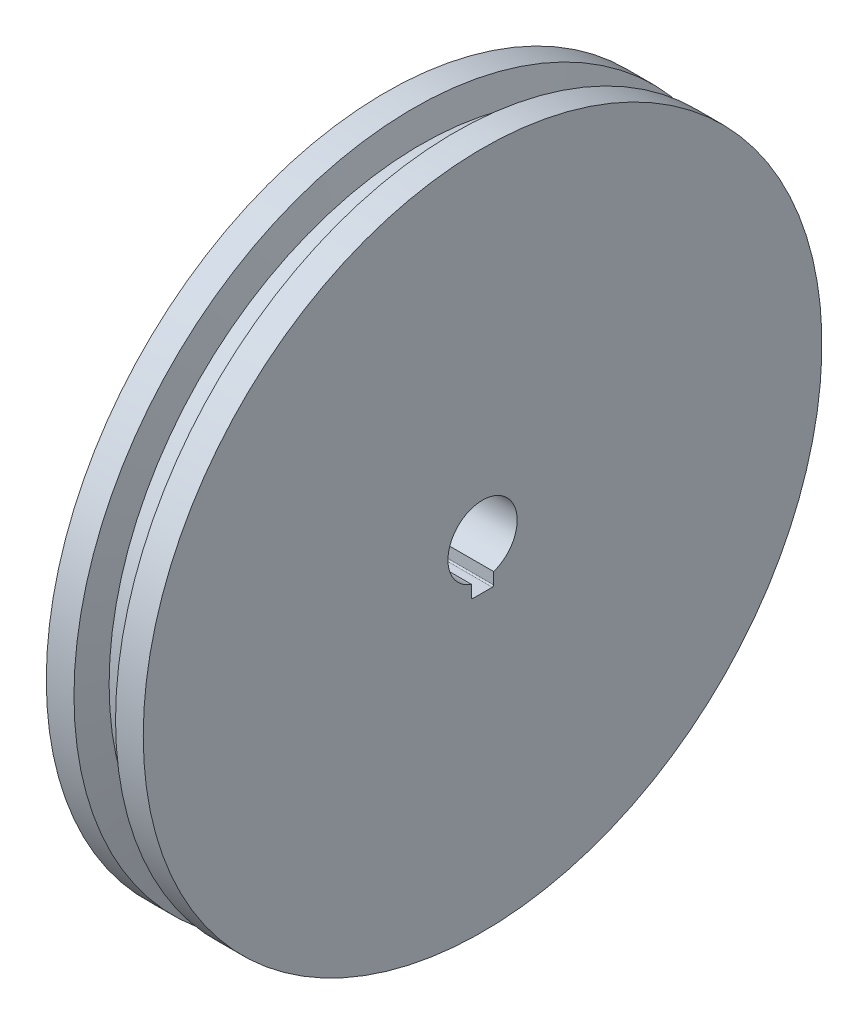
SolidWorks part; units mm, degrees
ref_plane "Front Plane" through (0, 0, 0) normal (0, 0, 1) x (1, 0, 0)
ref_plane "Top Plane" through (0, 0, 0) normal (0, 1, 0) x (1, 0, 0)
ref_plane "Right Plane" through (0, 0, 0) normal (1, 0, 0) x (0, 0, -1)
sketch "Sketch1" plane through (0, 0, 0) normal (0, 0, 1) x (1, 0, 0)
  line L0 (0, 0) -> (75, 0) construction
  line L1 (70, -12.5) -> (0, -12.5)
  line L2 (70, -122.5) -> (70, -12.5)
  line L3 (60, -122.5) -> (70, -122.5)
  line L4 (60, -122.5) -> (57.3205, -112.5)
  line L5 (57.3205, -112.5) -> (47.6795, -112.5)
  line L6 (47.6795, -112.5) -> (45, -122.5)
  line L7 (25, -30) -> (35, -30)
  line L8 (25, -30) -> (22.3205, -20)
  line L9 (22.3205, -20) -> (12.6795, -20)
  line L10 (12.6795, -20) -> (10, -30)
  line L11 (10, -30) -> (0, -30)
  line L12 (35, -30) -> (35, -122.5)
  line L13 (45, -122.5) -> (35, -122.5)
  line L16 (0, -30) -> (0, -12.5)
  dimension "D1" = 25
  dimension "D2" = 40
  dimension "D3" = 225
  dimension "D4" = 245
  dimension "D5" = 10
  dimension "D6" = 245
  dimension "D7" = 10
  dimension "D8" = 15
  dimension "D9" = 105
  dimension "D10" = 10
  dimension "D11" = 10
  dimension "D12" = 15
  dimension "D13" = 105
  dimension "D14" = 10
  dimension "D15" = 105
  dimension "D16" = 60
  dimension "D19" = 105
revolve "Revolve1" add sketch "Sketch1" angle 360 about L0
sketch "Esboço1" plane through (0, 0, 0) normal (-1, 0, 0) x (0, 0, 1)
  line L0 (0, 0) -> (0, -12.5) construction
  line L2 (3.5, -16.5) -> (-3.5, -16.5)
  line L3 (4, -16) -> (4, -8.5)
  line L4 (4, -8.5) -> (-4, -8.5)
  line L5 (-4, -16) -> (-4, -8.5)
  line L6 (4, -16.5) -> (-4, -8.5) construction
  line L7 (4, -8.5) -> (-4, -16.5) construction
  circle A0 centre (0, 0) radius 12.5 construction
  arc A1 (3.5, -16.5) -> (4, -16) centre (3.5, -16) ccw
  arc A2 (-3.5, -16.5) -> (-4, -16) centre (-3.5, -16) cw
  dimension "D3" = 0.5
  dimension "D1" = 8
  dimension "D2" = 8
extrude "Corte-extrusão1" cut sketch "Esboço1" against normal through all
